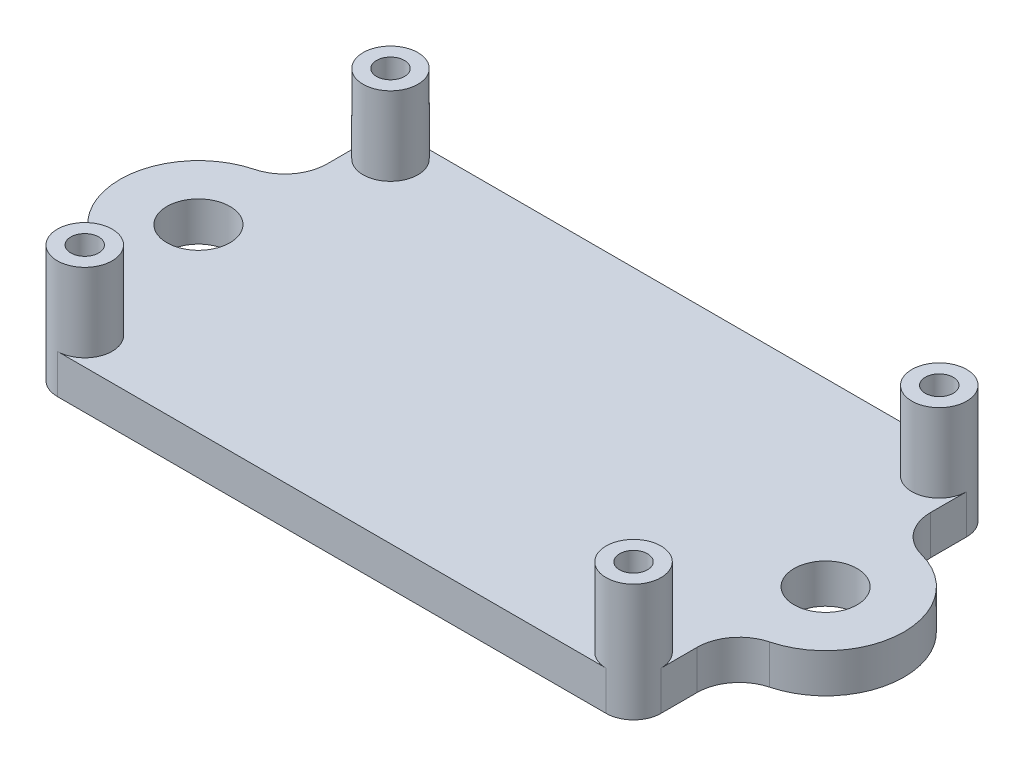
SolidWorks part; units mm, degrees
material "6061-T6 (SS)"
ref_plane "Front Plane" through (0, 0, 0) normal (0, 0, 1) x (1, 0, 0)
ref_plane "Top Plane" through (0, 0, 0) normal (0, 1, 0) x (1, 0, 0)
ref_plane "Right Plane" through (0, 0, 0) normal (1, 0, 0) x (0, 0, -1)
sketch "Sketch1" plane through (0, 0, 0) normal (0, 1, 0) x (1, 0, 0)
  line L0 (-25.4, 0) -> (0, 0) construction
  line L1 (-24.4475, 14.605) -> (24.4475, 14.605)
  line L2 (-24.4475, 14.605) -> (-24.4475, 6.2782)
  line L3 (-24.4475, -14.605) -> (24.4475, -14.605)
  line L4 (24.4475, 14.605) -> (24.4475, 6.2782)
  line L5 (-24.4475, 14.605) -> (24.4475, -14.605) construction
  line L6 (-24.4475, -14.605) -> (24.4475, 14.605) construction
  line L7 (0, 0) -> (25.4, 0) construction
  line L8 (-24.4475, -6.2782) -> (-24.4475, -14.605)
  line L9 (24.4475, -6.2782) -> (24.4475, -14.605)
  arc A0 (-24.4475, 6.2782) -> (-24.4475, -6.2782) centre (-25.4, 0) ccw
  arc A1 (24.4475, -6.2782) -> (24.4475, 6.2782) centre (25.4, 0) ccw
  point P0 (0, 0)
  dimension "D4" = 12.7
  dimension "D1" = 29.21
  dimension "D2" = 48.895
  dimension "D3" = 50.8
extrude "Boss-Extrude1" add sketch "Sketch1" along normal blind 3.175
fillet "Fillet1" radius 3.429 4 edges at (-24.4475, 1.5875, -6.2782) (24.4475, 1.5875, -6.2782) (-24.4475, 1.5875, 6.2782) (24.4475, 1.5875, 6.2782)
hole_wizard "#10 Clearance Hole1" positions "Sketch2" profile "Sketch3" hole size "#10" standard "ANSI Inch" end condition through all
sketch "Sketch2" plane through (0, 3.175, 0) normal (0, 1, 0) x (1, 0, 0)
  point P0 (25.4, 0)
  point P3 (-25.4, 0)
sketch "Sketch3" plane through (25.4, 3.175, 0) normal (1, 0, 0) x (0, 0, 1)
  line L0 (0, 0) -> (0, 3.175)
  line L1 (0, 3.175) -> (2.5527, 3.175)
  line L2 (2.5527, 3.175) -> (2.5527, 0)
  line L5 (2.5527, 0) -> (0, 0)
  line L11 (0, -6.35) -> (0, 107.95) construction
  dimension "Thru Hole Dia." = 5.1054
  dimension "Thru Hole Depth" = 3.175
sketch "Sketch4" plane through (0, 3.175, 0) normal (0, 1, 0) x (1, 0, 0)
  line L0 (-22.225, 12.3825) -> (22.225, -12.3825) construction
  line L1 (-1050.4953, -14.9225) -> (48949.5047, -14.9225) construction
  line L2 (-24.765, -992.6463) -> (-24.765, 49007.3537) construction
  line L3 (-24.4475, -14.605) -> (24.4475, -14.605) construction
  circle A0 centre (-22.225, 12.3825) radius 2.2225
  circle A1 centre (22.225, 12.3825) radius 2.2225
  circle A2 centre (22.225, -12.3825) radius 2.2225
  circle A3 centre (-22.225, -12.3825) radius 2.2225
  dimension "D2" = 2.54
  dimension "D3" = 2.54
  dimension "D4" = 46.99
  dimension "D5" = 27.305
extrude "Boss-Extrude2" add sketch "Sketch4" along normal blind 6.35
hole_wizard "#4-40 Tapped Hole1" positions "Sketch5" profile "Sketch6" tap size "#4-40" standard "ANSI Inch" end condition through all
sketch "Sketch5" plane through (0, 9.525, 0) normal (0, 1, 0) x (1, 0, 0)
  point P0 (22.225, 12.3825)
  point P3 (-22.225, 12.3825)
  point P6 (-22.225, -12.3825)
  point P9 (22.225, -12.3825)
sketch "Sketch6" plane through (22.225, 9.525, -12.3825) normal (1, 0, 0) x (0, 0, 1)
  line L0 (0, 0) -> (0, 9.525)
  line L1 (0, 9.525) -> (1.1303, 9.525)
  line L2 (1.1303, 9.525) -> (1.1303, 0)
  line L5 (1.1303, 0) -> (0, 0)
  line L11 (0, -6.35) -> (0, 107.95) construction
  dimension "Thru Tap Drill Dia." = 2.2606
  dimension "Thru Tap Drill Depth" = 9.525
cosmetic thread "Hole Thread1" parameters "D2"=2.8448
cosmetic thread "Hole Thread2" parameters "D2"=2.8448
cosmetic thread "Hole Thread3" parameters "D2"=2.8448
cosmetic thread "Hole Thread4" parameters "D2"=2.8448
sketch "Sketch7" plane through (0, 3.175, 0) normal (0, 1, 0) x (1, 0, 0)
  line L0 (-24.4475, -14.605) -> (-22.225, -14.605) construction
  line L1 (-24.4475, -12.3825) -> (-24.4475, -14.605) construction
  line L2 (-24.4475, -14.605) -> (-22.225, -14.605)
  line L3 (-24.4475, -12.3825) -> (-24.4475, -14.605)
  circle A0 centre (-22.225, -12.3825) radius 2.2225 construction
  arc A1 (-24.4475, -12.3825) -> (-22.225, -14.605) centre (-22.225, -12.3825) ccw
extrude "Cut-Extrude1" cut sketch "Sketch7" against normal through all
mirror "Mirror1" about plane through (0, 0, 0) normal (0, 0, 1) of "Cut-Extrude1"
mirror "Mirror2" about plane through (0, 0, 0) normal (1, 0, 0) of "Cut-Extrude1", "Mirror1"
